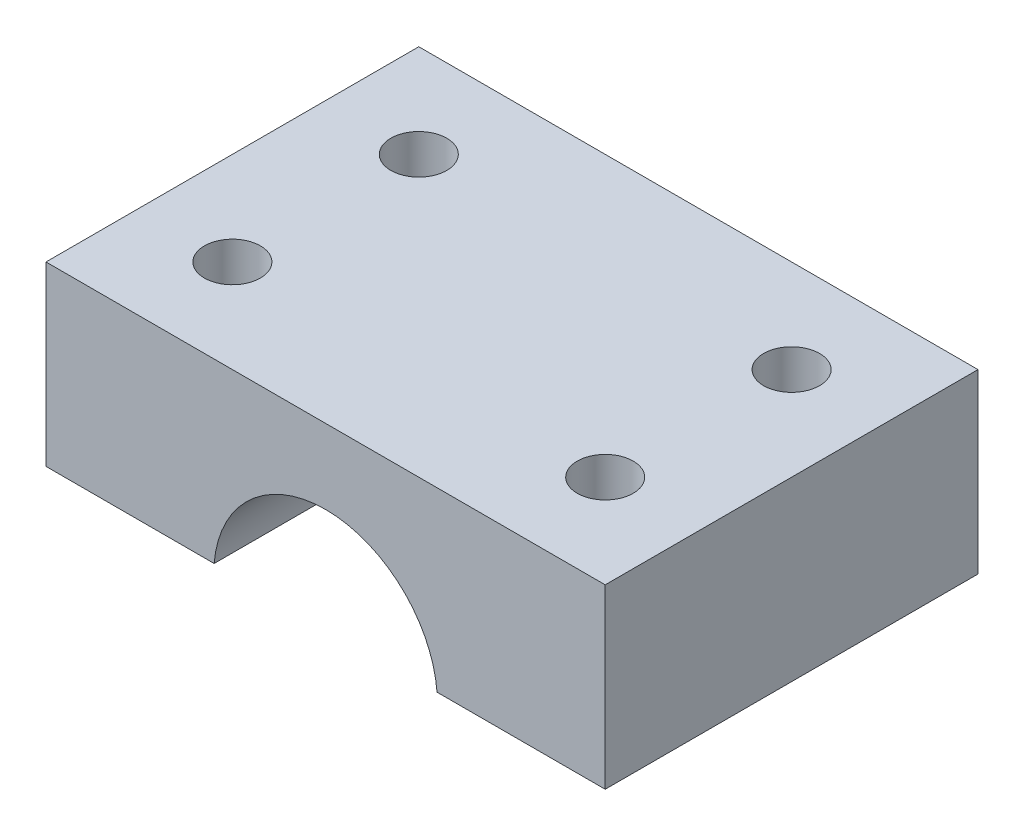
SolidWorks part; units mm, degrees
ref_plane "Plan de face" through (0, 0, 0) normal (0, 0, 1) x (1, 0, 0)
ref_plane "Plan de dessus" through (0, 0, 0) normal (0, 1, 0) x (1, 0, 0)
ref_plane "Plan de droite" through (0, 0, 0) normal (1, 0, 0) x (0, 0, -1)
sketch "Esquisse2" plane through (0, 0, 0) normal (0, 0, 1) x (1, 0, 0)
  line L0 (-5, 0.5) -> (-15, 0.5) construction
  line L1 (-15, 0.5) -> (-15, 10)
  line L2 (-15, 10) -> (15, 10)
  line L3 (15, 10) -> (15, 0.5)
  line L4 (15, 0.5) -> (5.9791, 0.5)
  line L5 (-15, 0.5) -> (-5.9791, 0.5)
  arc A0 (-5.9791, 0.5) -> (5.9791, 0.5) centre (0, 0) cw
  dimension "D3" = 6
  dimension "D1" = 9.5
  dimension "D2" = 30
  dimension "D5" = 15
  dimension "D6" = 10
extrude "Boss.-Extru.1" add sketch "Esquisse2" along normal blind 20
sketch "Esquisse3" plane through (0, 10, 0) normal (0, 1, 0) x (1, 0, 0)
  line L0 (-15, -20) -> (-15, 0) construction
  line L1 (15, 0) -> (-15, 0) construction
  line L2 (15, -20) -> (15, 0) construction
  line L3 (15, -20) -> (-15, -20) construction
  circle A0 centre (-10, -5) radius 1.5
  circle A1 centre (10, -5) radius 1.5
  circle A2 centre (-10, -15) radius 1.5
  circle A3 centre (10, -15) radius 1.5
  dimension "D2" = 3
  dimension "D6" = 3
  dimension "D9" = 3
  dimension "D12" = 3
  dimension "D1" = 5
  dimension "D3" = 5
  dimension "D4" = 5
  dimension "D5" = 5
  dimension "D7" = 5
  dimension "D8" = 5
  dimension "D10" = 5
  dimension "D11" = 5
extrude "Enlèv. mat.-Extru.1" cut sketch "Esquisse3" against normal blind 10
